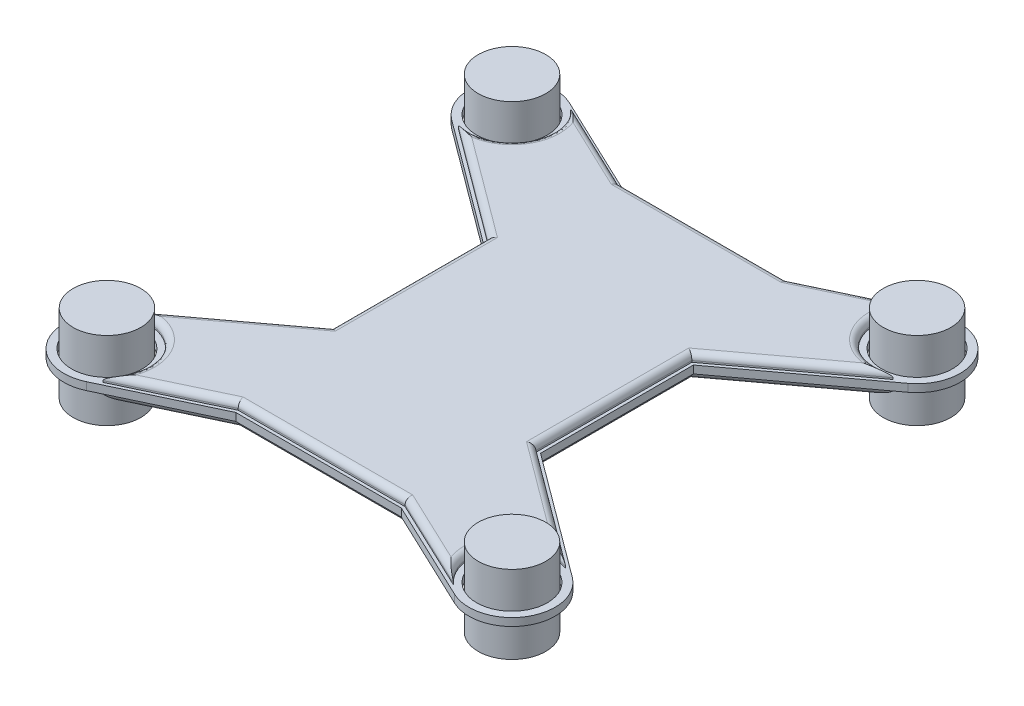
SolidWorks part; units mm, degrees
ref_plane "Front Plane" through (0, 0, 0) normal (0, 0, 1) x (1, 0, 0)
ref_plane "Top Plane" through (0, 0, 0) normal (0, 1, 0) x (1, 0, 0)
ref_plane "Right Plane" through (0, 0, 0) normal (1, 0, 0) x (0, 0, -1)
sketch "Sketch1" plane through (0, 0, 0) normal (0, 1, 0) x (1, 0, 0)
  line L1 (82.9978, -82.9978) -> (-82.9978, -82.9978) construction
  line L2 (82.9978, -82.9978) -> (82.9978, 82.9978) construction
  line L3 (82.9978, 82.9978) -> (-82.9978, 82.9978) construction
  line L4 (-82.9978, -82.9978) -> (-82.9978, 82.9978) construction
  line L5 (82.9978, -82.9978) -> (-82.9978, 82.9978) construction
  line L6 (82.9978, 82.9978) -> (-82.9978, -82.9978) construction
  circle A0 centre (-82.9978, 82.9978) radius 13.85
  circle A1 centre (82.9978, 82.9978) radius 13.85
  circle A2 centre (82.9978, -82.9978) radius 13.85
  circle A3 centre (-82.9978, -82.9978) radius 13.85
  point P0 (0, 0)
  dimension "D1" = 27.7
extrude "Boss-Extrude2" add sketch "Sketch1" along normal blind 32
ref_plane "Plane1" through (0, 16, 0) normal (0, 1, 0) x (1, 0, 0)
sketch "Sketch2" plane through (0, 16, 0) normal (0, 1, 0) x (1, 0, 0)
  line L0 (-93.523, -68.817) -> (-43.0131, -31.3278)
  line L1 (-75.4341, -98.956) -> (-33.9127, -79.2761)
  line L2 (75.4341, -98.956) -> (33.9127, -79.2761)
  line L3 (93.523, -68.817) -> (43.0131, -31.3278)
  line L4 (93.523, 68.817) -> (43.0131, 31.3278)
  line L5 (75.4341, 98.956) -> (33.9127, 79.2761)
  line L6 (-93.523, 68.817) -> (-43.0131, 31.3278)
  line L7 (-75.4341, 98.956) -> (-33.9127, 79.2761)
  line L17 (33.9127, -79.2761) -> (-33.9127, -79.2761)
  line L18 (33.9127, -79.2761) -> (33.9127, 79.2761)
  line L19 (33.9127, 79.2761) -> (-33.9127, 79.2761)
  line L20 (-33.9127, -79.2761) -> (-33.9127, 79.2761)
  line L21 (33.9127, -79.2761) -> (-33.9127, 79.2761) construction
  line L22 (33.9127, 79.2761) -> (-33.9127, -79.2761) construction
  line L23 (43.0131, -31.3278) -> (-43.0131, -31.3278)
  line L24 (43.0131, -31.3278) -> (43.0131, 31.3278)
  line L25 (43.0131, 31.3278) -> (-43.0131, 31.3278)
  line L26 (-43.0131, -31.3278) -> (-43.0131, 31.3278)
  line L27 (43.0131, -31.3278) -> (-43.0131, 31.3278) construction
  line L28 (43.0131, 31.3278) -> (-43.0131, -31.3278) construction
  arc A0 (-75.4341, 98.956) -> (-93.523, 68.817) centre (-82.9978, 82.9978) ccw
  circle A2 centre (-82.9978, 82.9978) radius 14.485
  circle A3 centre (82.9978, 82.9978) radius 14.485
  circle A4 centre (82.9978, -82.9978) radius 14.485
  circle A5 centre (-82.9978, -82.9978) radius 14.485
  circle A6 centre (-82.9978, -82.9978) radius 13.85 construction
  circle A7 centre (82.9978, -82.9978) radius 13.85 construction
  circle A8 centre (82.9978, 82.9978) radius 13.85 construction
  arc A9 (93.523, 68.817) -> (75.4341, 98.956) centre (82.9978, 82.9978) ccw
  arc A10 (75.4341, -98.956) -> (93.523, -68.817) centre (82.9978, -82.9978) ccw
  arc A11 (-93.523, -68.817) -> (-75.4341, -98.956) centre (-82.9978, -82.9978) ccw
  point P6 (0, 0)
  point P19 (0, 0)
  point P20 (0, 0)
  dimension "D1" = 28.97
  dimension "D2" = 35.32
extrude "Boss-Extrude3" add sketch "Sketch2" along normal mid plane 3.175 separate body contours L7 A0 L6 L25 L20 A2 | L26 L23 L20 L25 | L0 A11 L1 L20 L23 A5 | L18 L23 L20 L17 | L18 L25 L20 L23 | L25 L18 L19 L20 | L4 A9 L5 L18 L25 A3 | L24 L25 L18 L23 | L2 A10 L3 L23 L18 A4
sketch "Sketch3" plane through (0, 17.5875, 0) normal (0, 1, 0) x (1, 0, 0)
  line L24 (-34.1985, 78.0061) -> (-75.978, 97.8084)
  line L25 (-92.7661, 69.8368) -> (-41.7431, 31.9668)
  line L26 (-41.7431, 31.9668) -> (-41.7431, -31.9668)
  line L27 (-41.7431, -31.9668) -> (-92.7661, -69.8368)
  line L28 (-75.978, -97.8084) -> (-34.1985, -78.0061)
  line L29 (-34.1985, -78.0061) -> (34.1985, -78.0061)
  line L30 (34.1985, -78.0061) -> (75.978, -97.8084)
  line L31 (92.7661, -69.8368) -> (41.7431, -31.9668)
  line L32 (41.7431, -31.9668) -> (41.7431, 31.9668)
  line L33 (41.7431, 31.9668) -> (92.7661, 69.8368)
  line L34 (75.978, 97.8084) -> (34.1985, 78.0061)
  line L35 (34.1985, 78.0061) -> (-34.1985, 78.0061)
  line L36 (-34.1985, 78.0061) -> (-71.8155, 95.8355)
  line L37 (-89.0672, 67.0914) -> (-41.7431, 31.9668)
  line L38 (-41.7431, 31.9668) -> (-41.7431, -31.9668)
  line L39 (-41.7431, -31.9668) -> (-89.0672, -67.0914)
  line L40 (-71.8155, -95.8355) -> (-34.1985, -78.0061)
  line L41 (-34.1985, -78.0061) -> (34.1985, -78.0061)
  line L42 (34.1985, -78.0061) -> (71.8155, -95.8355)
  line L43 (89.0672, -67.0914) -> (41.7431, -31.9668)
  line L44 (41.7431, -31.9668) -> (41.7431, 31.9668)
  line L45 (41.7431, 31.9668) -> (89.0672, 67.0914)
  line L46 (71.8155, 95.8355) -> (34.1985, 78.0061)
  line L47 (34.1985, 78.0061) -> (-34.1985, 78.0061)
  arc A8 (-75.978, 97.8084) -> (-92.7661, 69.8368) centre (-82.9978, 82.9978) ccw
  arc A9 (-92.7661, -69.8368) -> (-75.978, -97.8084) centre (-82.9978, -82.9978) ccw
  arc A10 (75.978, -97.8084) -> (92.7661, -69.8368) centre (82.9978, -82.9978) ccw
  arc A11 (92.7661, 69.8368) -> (75.978, 97.8084) centre (82.9978, 82.9978) ccw
  circle A22 centre (82.9978, 82.9978) radius 17.025
  arc A23 (71.8155, 95.8355) -> (89.0672, 67.0914) centre (82.9978, 82.9978) ccw
  circle A31 centre (82.9978, -82.9978) radius 17.025
  arc A32 (89.0672, -67.0914) -> (71.8155, -95.8355) centre (82.9978, -82.9978) ccw
  circle A34 centre (-82.9978, -82.9978) radius 17.025
  arc A35 (-71.8155, -95.8355) -> (-89.0672, -67.0914) centre (-82.9978, -82.9978) ccw
  circle A37 centre (-82.9978, 82.9978) radius 17.025
  arc A38 (-89.0672, 67.0914) -> (-71.8155, 95.8355) centre (-82.9978, 82.9978) ccw
  dimension "D1" = 1.27
  dimension "D2" = 2.54
  dimension "D3" = 2.54
  dimension "D4" = 2.54
  dimension "D5" = 2.54
extrude "Boss-Extrude4" add sketch "Sketch3" along normal blind 3.175
fillet "Fillet1" radius 2.54 16 edges at (53.007, 20.7625, 86.9208) (0, 20.7625, 78.0061) (-53.007, 20.7625, 86.9208) (-68.4002, 20.7625, 74.2366) (-65.4051, 20.7625, 49.5291) (-41.7431, 20.7625, 0) (-65.4051, 20.7625, -49.5291) (-68.4002, 20.7625, -74.2366) (-53.007, 20.7625, -86.9208) (0, 20.7625, -78.0061) (53.007, 20.7625, -86.9208) (68.4002, 20.7625, -74.2366) (65.4051, 20.7625, -49.5291) (41.7431, 20.7625, 0) (65.4051, 20.7625, 49.5291) (68.4002, 20.7625, 74.2366)
mirror "Mirror1" about plane through (0, 16, 0) normal (0, 1, 0) of "Boss-Extrude4"
fillet "Fillet2" radius 2.54 16 edges at (65.4051, 11.2375, 49.5291) (41.7431, 11.2375, 0) (65.4051, 11.2375, -49.5291) (68.4002, 11.2375, -74.2366) (53.007, 11.2375, -86.9208) (0, 11.2375, -78.0061) (-53.007, 11.2375, -86.9208) (-68.4002, 11.2375, -74.2366) (-65.4051, 11.2375, -49.5291) (-41.7431, 11.2375, 0) (-65.4051, 11.2375, 49.5291) (-68.4002, 11.2375, 74.2366) (-53.007, 11.2375, 86.9208) (0, 11.2375, 78.0061) (53.007, 11.2375, 86.9208) (68.4002, 11.2375, 74.2366)
